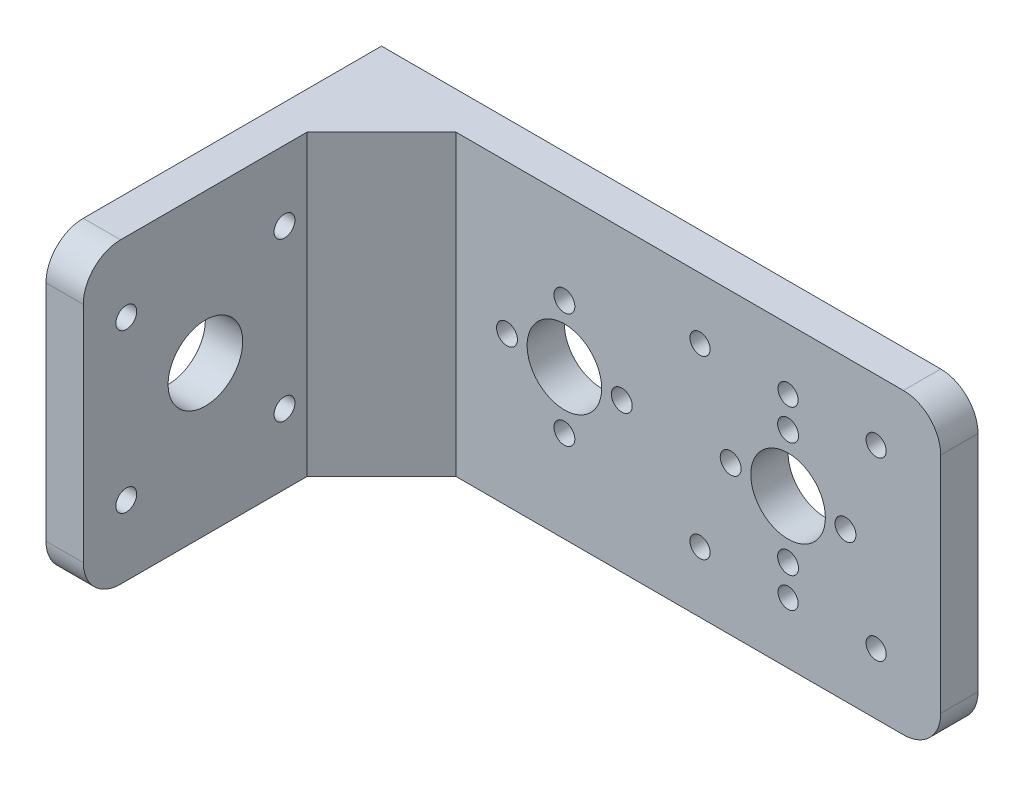
SolidWorks part; units mm, degrees
material "Copper"
ref_plane "Front Plane" through (0, 0, 0) normal (0, 0, 1) x (1, 0, 0)
ref_plane "Top Plane" through (0, 0, 0) normal (0, 1, 0) x (1, 0, 0)
ref_plane "Right Plane" through (0, 0, 0) normal (1, 0, 0) x (0, 0, -1)
sketch "Sketch1" plane through (0, 0, 0) normal (0, 0, 1) x (1, 0, 0)
  line L1 (0, 0) -> (-101.6, 0)
  line L2 (0, 0) -> (0, -50.8)
  line L3 (0, -50.8) -> (-101.6, -50.8)
  line L4 (-101.6, 0) -> (-101.6, -50.8)
  dimension "D1" = 50.8
  dimension "D2" = 101.6
extrude "Boss-Extrude1" add sketch "Sketch1" along normal blind 6.35
sketch "Sketch2" plane through (0, 0, 6.35) normal (0, 0, 1) x (1, 0, 0)
  line L0 (0, -25.4) -> (-101.6, -25.4) construction
  line L3 (0, -50.8) -> (0, 0) construction
  line L4 (-101.6, 0) -> (-101.6, -50.8) construction
  circle A0 centre (-11, -10.4) radius 1.7145
  circle A1 centre (-41, -10.4) radius 1.7145
  circle A2 centre (-41, -40.4) radius 1.7145
  circle A3 centre (-11, -40.4) radius 1.7145
  circle A4 centre (-26, -40.4) radius 1.7145
  circle A5 centre (-26, -10.4) radius 1.7145
  dimension "D1" = 15
  dimension "D7" = 3.429
  dimension "D8" = 3.429
  dimension "D9" = 3.429
  dimension "D10" = 3.429
  dimension "D13" = 3.429
  dimension "D14" = 3.429
  dimension "D2" = 15
  dimension "D3" = 15
  dimension "D4" = 15
  dimension "D5" = 30
  dimension "D6" = 30
  dimension "D11" = 11
  dimension "D12" = 11
  dimension "D15" = 15
  dimension "D16" = 15
  dimension "D17" = 15
  dimension "D18" = 15
extrude "Cut-Extrude1" cut sketch "Sketch2" against normal blind 6.35
sketch "Sketch3" plane through (0, 0, 6.35) normal (0, 0, 1) x (1, 0, 0)
  line L0 (0, -25.4) -> (-101.6, -25.4) construction
  line L1 (0, -50.8) -> (0, 0) construction
  line L2 (-101.6, 0) -> (-101.6, -50.8) construction
  circle A0 centre (-26, -15.621) radius 1.778
  dimension "D1" = 26
  dimension "D3" = 3.556
  dimension "D2" = 9.779
extrude "Cut-Extrude2" cut sketch "Sketch3" against normal blind 6.35
sketch "Sketch4" plane through (0, 0, 6.35) normal (0, 0, 1) x (1, 0, 0)
  line L0 (0, -25.4) -> (-101.6, -25.4) construction
  line L3 (0, -50.8) -> (0, 0) construction
  line L4 (-101.6, 0) -> (-101.6, -50.8) construction
  circle A0 centre (-26, -25.4) radius 6.35
  dimension "D1" = 12.7
  dimension "D2" = 26
extrude "Cut-Extrude3" cut sketch "Sketch4" against normal blind 6.35
pattern_circular "CirPattern1" count 4 over 360 about axis through (-26, -25.4, 0) along (0, 0, 1) of "Cut-Extrude2"
sketch "Sketch5" plane through (0, 0, 6.35) normal (0, 0, 1) x (1, 0, 0)
  line L0 (-101.6, -50.8) -> (0, -50.8) construction
  line L1 (-101.6, 0) -> (-95.25, 0)
  line L2 (-101.6, 0) -> (-101.6, -50.8)
  line L3 (-101.6, -50.8) -> (-95.25, -50.8)
  line L4 (-95.25, 0) -> (-95.25, -50.8)
  dimension "D1" = 6.35
extrude "Boss-Extrude2" add sketch "Sketch5" along normal blind 50.8
sketch "Sketch6" plane through (-95.25, 0, 0) normal (1, 0, 0) x (0, 0, -1)
  line L0 (-6.35, -50.8) -> (-6.35, 0) construction
  line L1 (-57.15, -50.8) -> (-6.35, -50.8) construction
  circle A0 centre (-36.35, -25.4) radius 6.35
  dimension "D1" = 30
  dimension "D2" = 12.7
  dimension "D3" = 25.4
extrude "Cut-Extrude4" cut sketch "Sketch6" against normal blind 6.35
sketch "Sketch7" plane through (-95.25, 0, 0) normal (1, 0, 0) x (0, 0, -1)
  circle A0 centre (-49.8247, -11.9253) radius 1.778
  circle A1 centre (-36.35, -25.4) radius 6.35 construction
  dimension "D1" = 3.556
  dimension "D2" = 13.4747
  dimension "D3" = 13.4747
extrude "Cut-Extrude5" cut sketch "Sketch7" against normal blind 6.35
pattern_circular "CirPattern2" count 4 over 360 about axis through (0, -25.4, 36.35) along (1, 0, 0) of "Cut-Extrude5"
pattern_linear "LPattern1" count 2 spacing 38.1 along (-1, 0, 0) of "CirPattern1", "Cut-Extrude3", "Cut-Extrude2"
sketch "Sketch8" plane through (0, -50.8, 0) normal (0, -1, 0) x (1, 0, 0)
  line L0 (-95.25, 6.35) -> (-95.25, 19.05)
  line L1 (-95.25, 57.15) -> (-95.25, 6.35) construction
  line L2 (-95.25, 19.05) -> (-82.55, 6.35)
  line L3 (-95.25, 6.35) -> (0, 6.35) construction
  line L4 (-82.55, 6.35) -> (-95.25, 6.35)
  dimension "D1" = 12.7
  dimension "D2" = 12.7
extrude "Boss-Extrude3" add sketch "Sketch8" against normal blind 50.8
fillet "Fillet1" radius 6.35 4 edges at (0, -50.8, 3.175) (0, 0, 3.175) (-98.425, 0, 57.15) (-98.425, -50.8, 57.15)
